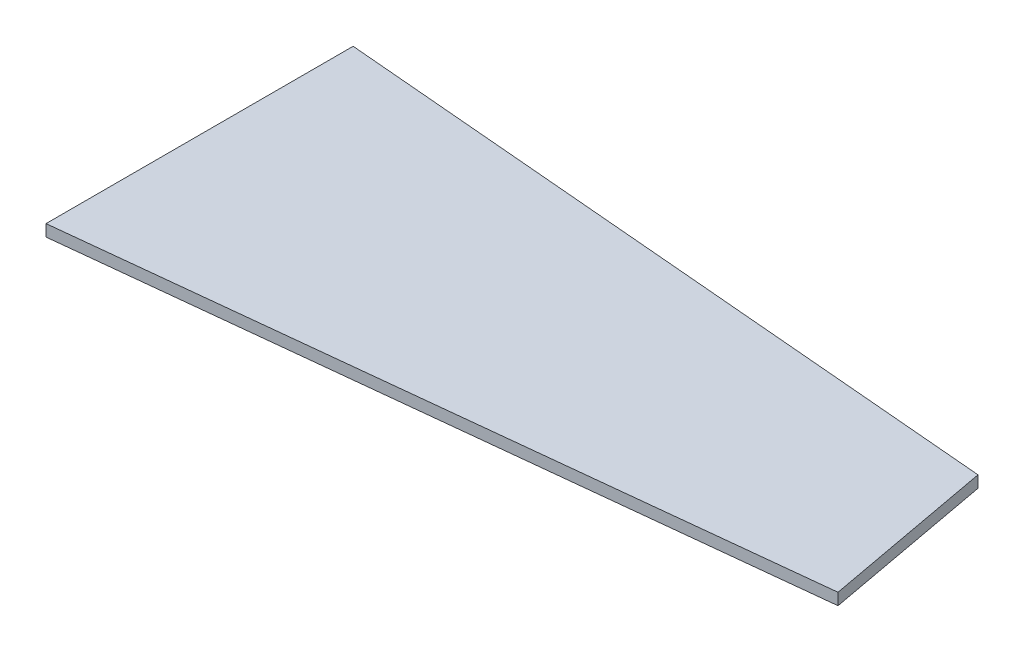
SolidWorks part; units mm, degrees
ref_plane "Plan de face" through (0, 0, 0) normal (0, 0, 1) x (1, 0, 0)
ref_plane "Plan de dessus" through (0, 0, 0) normal (0, 1, 0) x (1, 0, 0)
ref_plane "Plan de droite" through (0, 0, 0) normal (1, 0, 0) x (0, 0, -1)
sketch "Esquisse1" plane through (0, 0, 0) normal (0, 1, 0) x (1, 0, 0)
  line L0 (117.1053, 42.564) -> (0, 52.619)
  line L1 (0, 52.619) -> (0, 0)
  line L2 (0, 0) -> (122.5402, 13.1471)
  line L3 (122.5402, 13.1471) -> (117.1053, 42.564)
  point P4 (0, 0)
extrude "Boss.-Extru.1" add sketch "Esquisse1" along normal blind 2
